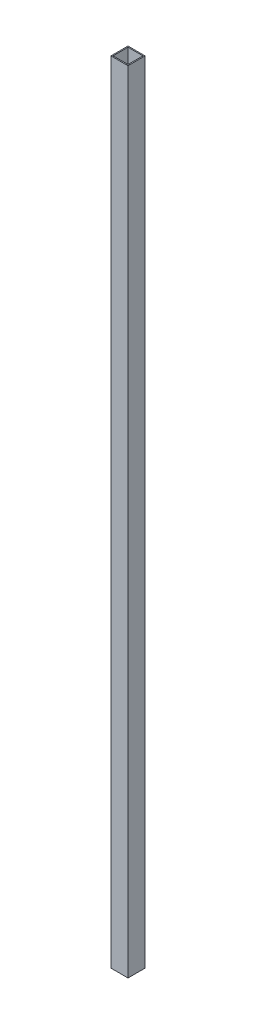
SolidWorks part; units mm, degrees
material "Zoltek Panex 33"
ref_plane "Front Plane" through (0, 0, 0) normal (0, 0, 1) x (1, 0, 0)
ref_plane "Top Plane" through (0, 0, 0) normal (0, 1, 0) x (1, 0, 0)
ref_plane "Right Plane" through (0, 0, 0) normal (1, 0, 0) x (0, 0, -1)
sketch "Sketch1" plane through (0, 0, 0) normal (0, 1, 0) x (1, 0, 0)
  line L0 (0.5, 0.5) -> (7.5, 0.5)
  line L1 (0, 0) -> (8, 0)
  line L2 (0, 0) -> (0, 8)
  line L3 (0, 8) -> (8, 8)
  line L4 (8, 0) -> (8, 8)
  line L5 (7.5, 0.5) -> (7.5, 7.5)
  line L6 (0.5, 7.5) -> (7.5, 7.5)
  line L7 (0.5, 0.5) -> (0.5, 7.5)
  dimension "D1" = 8
  dimension "D2" = 7
extrude "Boss-Extrude1" add sketch "Sketch1" along normal blind 370
